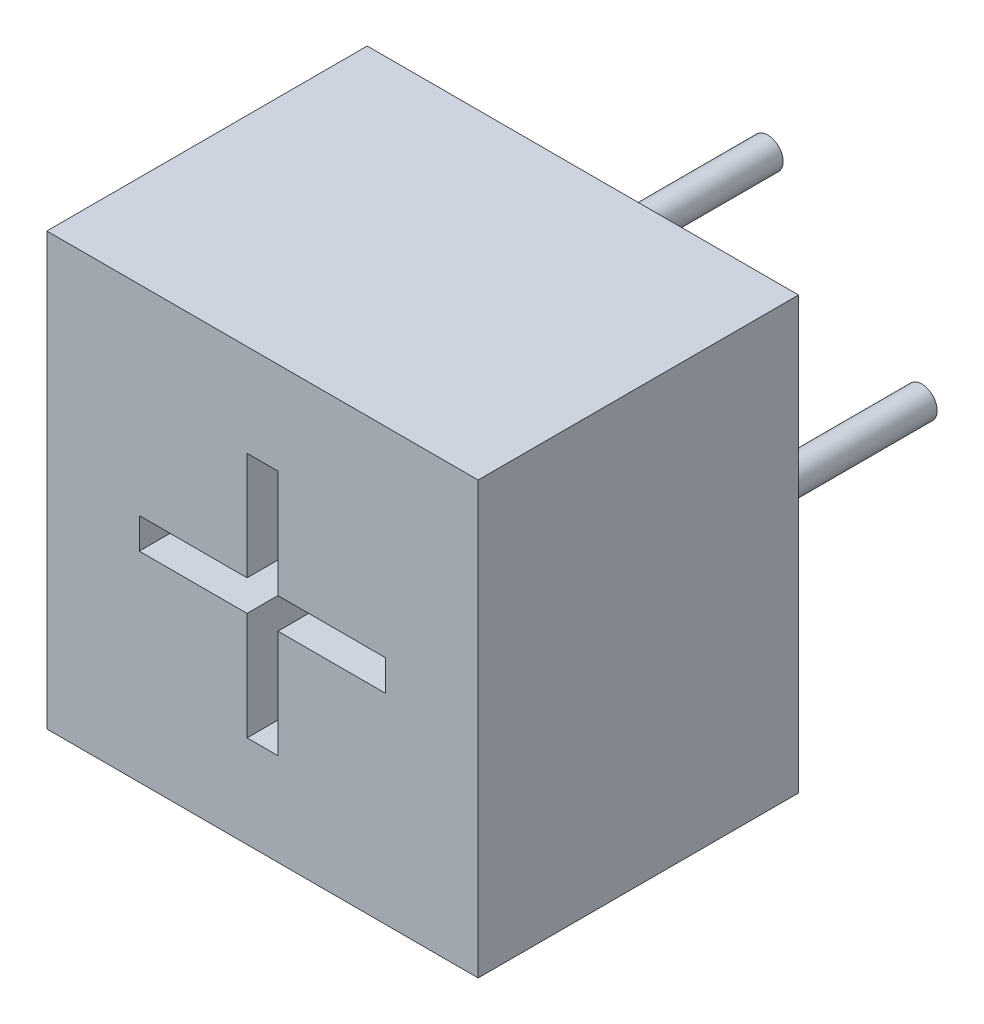
SolidWorks part; units mm, degrees
ref_plane "前视基准面" through (0, 0, 0) normal (0, 0, 1) x (1, 0, 0)
ref_plane "上视基准面" through (0, 0, 0) normal (0, 1, 0) x (1, 0, 0)
ref_plane "右视基准面" through (0, 0, 0) normal (1, 0, 0) x (0, 0, -1)
sketch "Sketch1" plane through (0, 0, 0) normal (0, 0, 1) x (1, 0, 0)
  line L1 (-3.5, -3.5) -> (3.5, -3.5)
  line L2 (-3.5, -3.5) -> (-3.5, 3.5)
  line L3 (-3.5, 3.5) -> (3.5, 3.5)
  line L4 (3.5, -3.5) -> (3.5, 3.5)
  line L5 (-3.5, -3.5) -> (3.5, 3.5) construction
  line L6 (-3.5, 3.5) -> (3.5, -3.5) construction
  point P0 (0, 0)
  dimension "D1" = 7
  dimension "D2" = 7
extrude "Boss-Extrude1" add sketch "Sketch1" along normal blind 5.2
sketch "Sketch2" plane through (0, 0, 5.2) normal (0, 0, 1) x (1, 0, 0)
  line L5 (2, -0.25) -> (-2, -0.25)
  line L6 (2, -0.25) -> (2, 0.25)
  line L11 (2, 0.25) -> (-2, 0.25)
  line L12 (-2, -0.25) -> (-2, 0.25)
  line L17 (2, -0.25) -> (-2, 0.25) construction
  line L18 (2, 0.25) -> (-2, -0.25) construction
  line L19 (0.25, -2) -> (-0.25, -2)
  line L20 (0.25, -2) -> (0.25, 2)
  line L21 (0.25, 2) -> (-0.25, 2)
  line L22 (-0.25, -2) -> (-0.25, 2)
  line L23 (0.25, -2) -> (-0.25, 2) construction
  line L24 (0.25, 2) -> (-0.25, -2) construction
  point P0 (0, 0)
  point P6 (0, 0)
  dimension "D1" = 0.5
  dimension "D2" = 0.5
  dimension "D3" = 4
  dimension "D4" = 4
extrude "Cut-Extrude1" cut sketch "Sketch2" against normal blind 2 contours L20 L5 L6 L11 | L22 L11 L20 L21 | L22 L5 L20 L11 | L22 L19 L20 L5
sketch "Sketch3" plane through (0, 0, 0) normal (0, 0, -1) x (-1, 0, 0)
  line L0 (-3.5, 3.5) -> (3.5, 3.5) construction
  circle A0 centre (0, 2.25) radius 0.25
  circle A1 centre (2.5, 0) radius 0.25
  circle A2 centre (-2.5, 0) radius 0.25
  dimension "D1" = 0.5
  dimension "D2" = 0.5
  dimension "D3" = 0.5
  dimension "D4" = 1.25
  dimension "D5" = 2.5
  dimension "D6" = 2.5
extrude "Boss-Extrude2" add sketch "Sketch3" along normal blind 3
equation "\"4、\"=5.07138"
